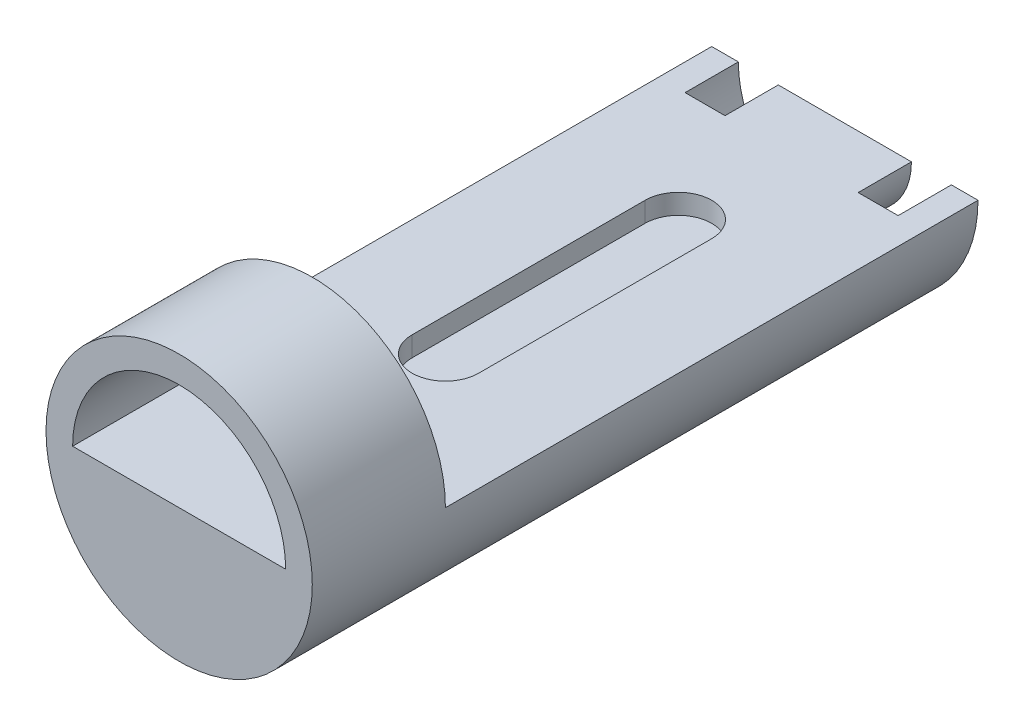
SolidWorks part; units mm, degrees
ref_plane "Front Plane" through (0, 0, 0) normal (0, 0, 1) x (1, 0, 0)
ref_plane "Top Plane" through (0, 0, 0) normal (0, 1, 0) x (1, 0, 0)
ref_plane "Right Plane" through (0, 0, 0) normal (1, 0, 0) x (0, 0, -1)
sketch "Sketch1" plane through (0, 0, 0) normal (0, 0, 1) x (1, 0, 0)
  line L1 (-20, 0) -> (-16, 0)
  line L2 (-16, 0) -> (-10, 0)
  line L3 (-10, 0) -> (0, 0)
  line L4 (0, 0) -> (10, 0)
  line L5 (10, 0) -> (16, 0)
  line L6 (16, 0) -> (20, 0)
  arc A3 (-20, 0) -> (20, 0) centre (0, 0) ccw
  dimension "D3" = 40
extrude "Boss-Extrude1" add sketch "Sketch1" along normal blind 100
sketch "Sketch2" plane through (0, 0, 0) normal (0, 0, -1) x (-1, 0, 0)
  line L0 (-16, 0) -> (16, 0)
  arc A0 (-16, 0) -> (16, 0) centre (0, 0) ccw
  arc A1 (-10, 0) -> (10, 0) centre (0, 0) ccw
  line M2 (20, 0) -> (-20, 0)
  dimension "D1" = 32
  dimension "D2" = 20
extrude "Cut-Extrude1" cut sketch "Sketch2" against normal blind 8 contours A1 A0 M2
sketch "Sketch3" plane through (0, 0, 0) normal (0, 1, 0) x (1, 0, 0)
  line L0 (0, -25) -> (0, -60) construction
  line L1 (5, -25) -> (5, -60)
  line L2 (-5, -25) -> (-5, -60)
  line L3 (10, 0) -> (-10, 0) construction
  arc A0 (5, -25) -> (-5, -25) centre (0, -25) ccw
  arc A1 (-5, -60) -> (5, -60) centre (0, -60) ccw
  point P3 (0, -42.5)
  dimension "D1" = 10
  dimension "D2" = 35
  dimension "D3" = 25
extrude "Cut-Extrude2" cut sketch "Sketch3" against normal blind 3 contours L2 A1 L1 A0
sketch "Sketch4" plane through (0, 0, 100) normal (0, 0, 1) x (1, 0, 0)
  line L1 (-16, 0) -> (16, 0)
  line L2 (20, 0) -> (-20, 0) construction
  line L3 (-16, 0) -> (-20, 0)
  line L4 (16, 0) -> (20, 0)
  arc A0 (20, 0) -> (-20, 0) centre (0, 0) ccw
  arc A1 (-20, 0) -> (20, 0) centre (0, 0) ccw construction
  arc A2 (16, 0) -> (-16, 0) centre (0, 0) ccw
  line M3 (20, 0) -> (-20, 0)
  dimension "D1" = 32
extrude "Boss-Extrude4" add sketch "Sketch4" against normal blind 20 contours A2 A0 M3
